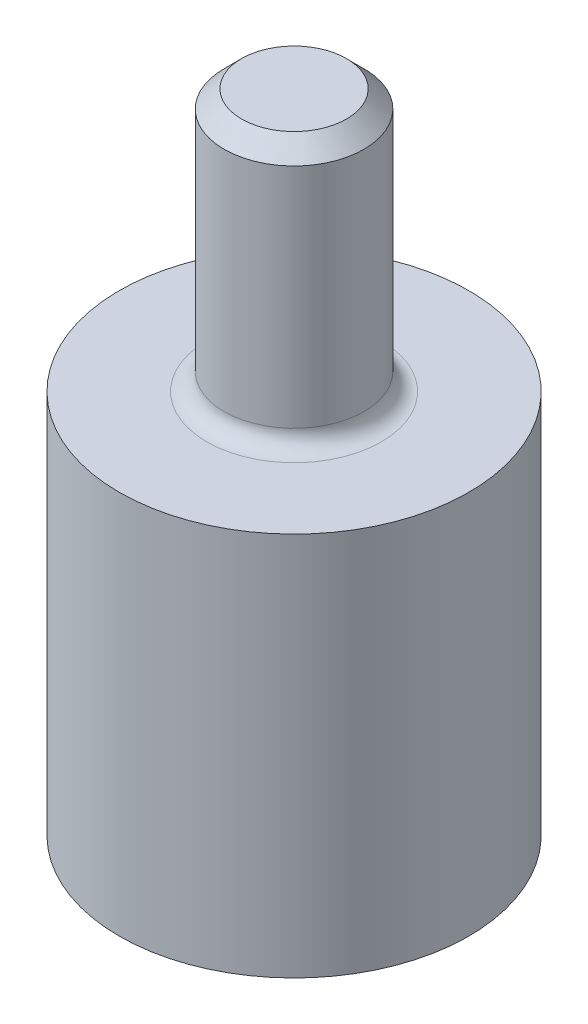
SolidWorks part; units mm, degrees
ref_plane "前视基准面" through (0, 0, 0) normal (0, 0, 1) x (1, 0, 0)
ref_plane "上视基准面" through (0, 0, 0) normal (0, 1, 0) x (1, 0, 0)
ref_plane "右视基准面" through (0, 0, 0) normal (1, 0, 0) x (0, 0, -1)
sketch "草图1" plane through (0, 0, 0) normal (0, 1, 0) x (1, 0, 0)
  circle A0 centre (0, 0) radius 10
  dimension "D1" = 20
extrude "凸台-拉伸1" add sketch "草图1" along normal blind 22
sketch "草图2" plane through (0, 22, 0) normal (0, 1, 0) x (1, 0, 0)
  circle A0 centre (0, 0) radius 4
extrude "凸台-拉伸2" add sketch "草图2" along normal blind 15
fillet "圆角1" radius 1 1 edges at (0, 22, 4)
chamfer "倒角1" distance 1 angle 45 1 edges at (0, 37, 4)
sketch "草图4" plane through (0, 0, 0) normal (0, -1, 0) x (1, 0, 0)
  circle A0 centre (0, 0) radius 3
extrude "切除-拉伸1" cut sketch "草图4" against normal blind 16
sketch "草图3" plane through (0, 0, 0) normal (0, 0, 1) x (1, 0, 0)
  line L0 (-10, 0) -> (10, 0) construction
  circle A0 centre (0, 4) radius 1.35
  dimension "D1" = 4
extrude "切除-拉伸2" cut sketch "草图3" against normal blind 10
sketch "草图5" plane through (0, 0, 0) normal (1, 0, 0) x (0, 0, -1)
  line L0 (0, 22) -> (0, 0) construction
  line L1 (-10, 0) -> (10, 0) construction
  circle A0 centre (0, 4) radius 1.35
  dimension "D1" = 4
extrude "切除-拉伸3" cut sketch "草图5" against normal blind 10
